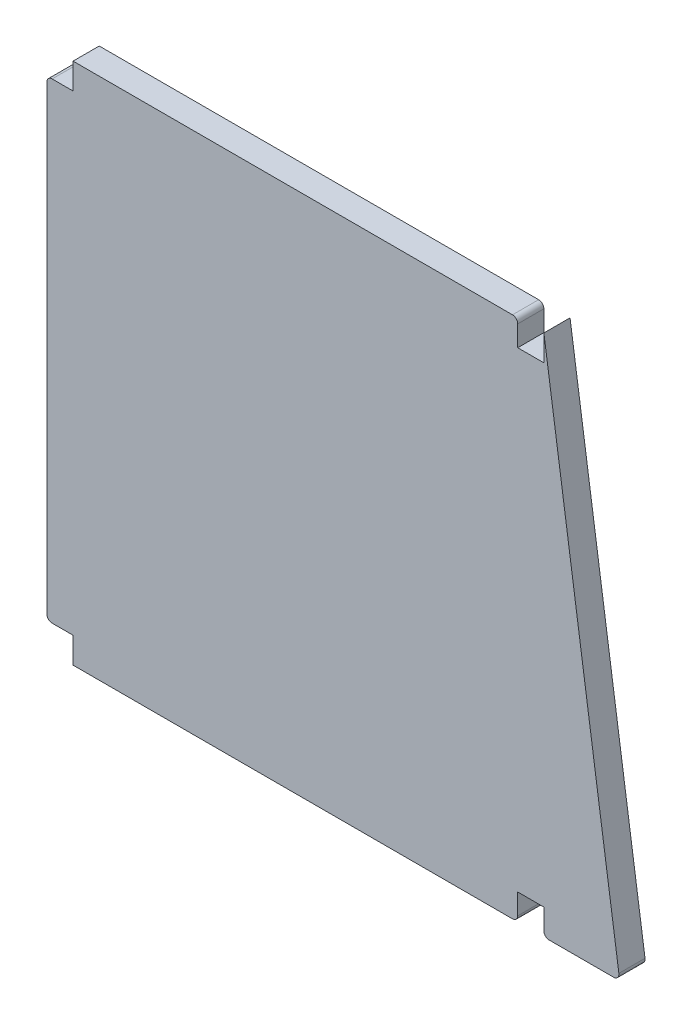
SolidWorks part; units mm, degrees
ref_plane "Front" through (0, 0, 0) normal (0, 0, 1) x (1, 0, 0)
ref_plane "Top" through (0, 0, 0) normal (0, 1, 0) x (1, 0, 0)
ref_plane "Right" through (0, 0, 0) normal (1, 0, 0) x (0, 0, -1)
sketch "Sketch1" plane through (0, 0, 0) normal (0, 0, 1) x (1, 0, 0)
  line L0 (0, 95.05) -> (0, 100)
  line L1 (0, 0) -> (85, 0)
  line L2 (0, 0) -> (0, 4.95)
  line L3 (0, 100) -> (85, 100)
  line L4 (85, 0) -> (85, 4.95)
  line L5 (0, 95.05) -> (-5, 95.05)
  line L7 (0, 4.95) -> (-5, 4.95)
  line L8 (-5, 95.05) -> (-5, 4.95)
  line L9 (85, 95.05) -> (90, 95.05)
  line L11 (85, 4.95) -> (90, 4.95)
  line L13 (85, 95.05) -> (85, 100)
  line L14 (90, 4.95) -> (90, 0)
  line L15 (90, 0) -> (104.5, 0)
  line L16 (104.5, 0) -> (90, 100)
  line L17 (90, 100) -> (90, 95.05)
  point P13 (-2.5, 95.05)
  dimension "D1" = 85
  dimension "D2" = 4.95
  dimension "D3" = 4.95
  dimension "D4" = 4.95
  dimension "D5" = 5
  dimension "D6" = 4.95
  dimension "D7" = 100
  dimension "D8" = 5
  dimension "D9" = 14.5
extrude "Boss-Extrude1" add sketch "Sketch1" along normal blind 5
fillet "Fillet1" radius 1 6 edges at (85, 100, 2.5) (104.5, 0, 2.5) (90, 0, 2.5) (85, 0, 2.5) (-5, 4.95, 2.5) (-5, 95.05, 2.5)
